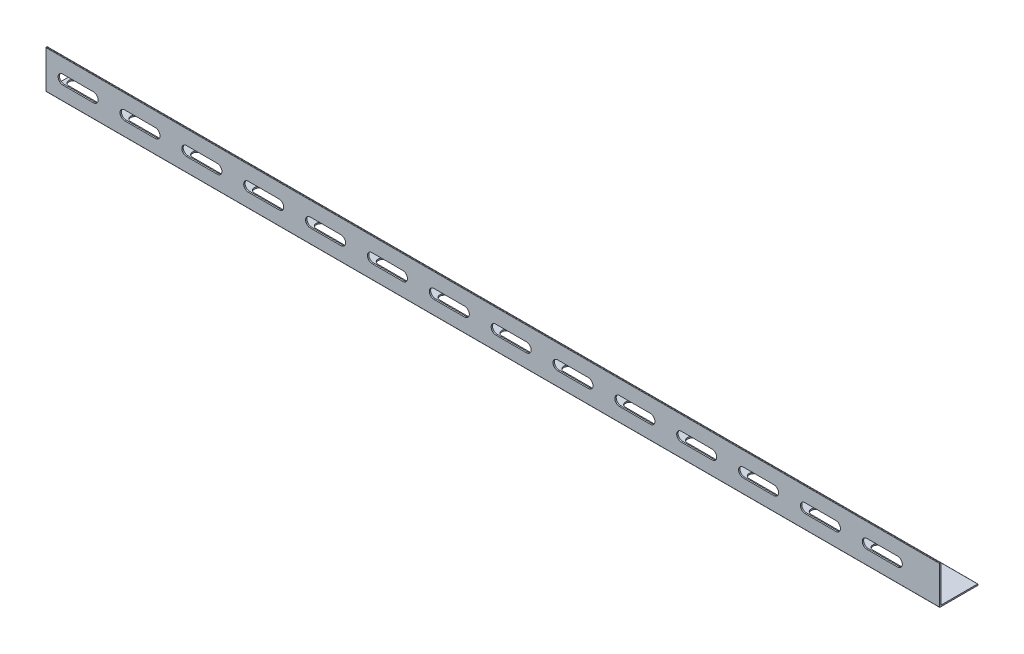
SolidWorks part; units mm, degrees
ref_plane "前视基准面" through (0, 0, 0) normal (0, 0, 1) x (1, 0, 0)
ref_plane "上视基准面" through (0, 0, 0) normal (0, 1, 0) x (1, 0, 0)
ref_plane "右视基准面" through (0, 0, 0) normal (1, 0, 0) x (0, 0, -1)
other "Configuration Table"
sketch "草图1" plane through (0, 0, 0) normal (1, 0, 0) x (0, 0, -1)
  line L1 (0, 0) -> (-5.4814, 0)
  line L2 (-4.7814, 1.3) -> (-4.7814, 27.7)
  line L3 (-5.0814, 28) -> (-5.4814, 28)
  line L4 (-5.7814, 0.3) -> (-5.7814, 27.7)
  line L5 (0, 0) -> (21.9186, 0)
  line L7 (-4.4814, 1) -> (21.9186, 1)
  line L8 (22.2186, 0.3) -> (22.2186, 0.7)
  arc A0 (-4.7814, 27.7) -> (-5.0814, 28) centre (-5.0814, 27.7) ccw
  arc A1 (-5.4814, 28) -> (-5.7814, 27.7) centre (-5.4814, 27.7) ccw
  arc A2 (21.9186, 0) -> (22.2186, 0.3) centre (21.9186, 0.3) ccw
  arc A3 (21.9186, 1) -> (22.2186, 0.7) centre (21.9186, 0.7) cw
  arc A4 (-4.7814, 1.3) -> (-4.4814, 1) centre (-4.4814, 1.3) ccw
  arc A5 (-5.4814, 0) -> (-5.7814, 0.3) centre (-5.4814, 0.3) cw
  point P10 (-4.7814, 28)
  point P13 (-5.7814, 28)
  point P16 (22.2186, 0)
  point P19 (22.2186, 1)
  point P24 (-5.7814, 0)
  dimension "D5" = 0.3
  dimension "D1" = 28
  dimension "D2" = 28
  dimension "D3" = 1
  dimension "D4" = 1
extrude "凸台-拉伸1" add sketch "草图1" along normal blind 650
sketch "草图2" plane through (0, 0, 5.7814) normal (0, 0, 1) x (1, 0, 0)
  line L0 (12.2523, 13.7143) -> (34.5086, 13.7143) construction
  line L1 (12.2523, 17.1497) -> (34.5086, 17.1497)
  line L2 (12.2523, 10.279) -> (34.5086, 10.279)
  line L3 (57.2523, 13.7143) -> (79.5086, 13.7143) construction
  line L4 (57.2523, 17.1497) -> (79.5086, 17.1497)
  line L5 (57.2523, 10.279) -> (79.5086, 10.279)
  line L6 (102.2523, 13.7143) -> (124.5086, 13.7143) construction
  line L7 (102.2523, 17.1497) -> (124.5086, 17.1497)
  line L8 (102.2523, 10.279) -> (124.5086, 10.279)
  line L9 (147.2523, 13.7143) -> (169.5086, 13.7143) construction
  line L10 (147.2523, 17.1497) -> (169.5086, 17.1497)
  line L11 (147.2523, 10.279) -> (169.5086, 10.279)
  line L12 (192.2523, 13.7143) -> (214.5086, 13.7143) construction
  line L13 (192.2523, 17.1497) -> (214.5086, 17.1497)
  line L14 (192.2523, 10.279) -> (214.5086, 10.279)
  line L15 (237.2523, 13.7143) -> (259.5086, 13.7143) construction
  line L16 (237.2523, 17.1497) -> (259.5086, 17.1497)
  line L17 (237.2523, 10.279) -> (259.5086, 10.279)
  line L18 (282.2523, 13.7143) -> (304.5086, 13.7143) construction
  line L19 (282.2523, 17.1497) -> (304.5086, 17.1497)
  line L20 (282.2523, 10.279) -> (304.5086, 10.279)
  line L21 (327.2523, 13.7143) -> (349.5086, 13.7143) construction
  line L22 (327.2523, 17.1497) -> (349.5086, 17.1497)
  line L23 (327.2523, 10.279) -> (349.5086, 10.279)
  line L24 (372.2523, 13.7143) -> (394.5086, 13.7143) construction
  line L25 (372.2523, 17.1497) -> (394.5086, 17.1497)
  line L26 (372.2523, 10.279) -> (394.5086, 10.279)
  line L27 (417.2523, 13.7143) -> (439.5086, 13.7143) construction
  line L28 (417.2523, 17.1497) -> (439.5086, 17.1497)
  line L29 (417.2523, 10.279) -> (439.5086, 10.279)
  line L30 (462.2523, 13.7143) -> (484.5086, 13.7143) construction
  line L31 (462.2523, 17.1497) -> (484.5086, 17.1497)
  line L32 (462.2523, 10.279) -> (484.5086, 10.279)
  line L33 (507.2523, 13.7143) -> (529.5086, 13.7143) construction
  line L34 (507.2523, 17.1497) -> (529.5086, 17.1497)
  line L35 (507.2523, 10.279) -> (529.5086, 10.279)
  line L36 (552.2523, 13.7143) -> (574.5086, 13.7143) construction
  line L37 (552.2523, 17.1497) -> (574.5086, 17.1497)
  line L38 (552.2523, 10.279) -> (574.5086, 10.279)
  line L39 (597.2523, 13.7143) -> (619.5086, 13.7143) construction
  line L40 (597.2523, 17.1497) -> (619.5086, 17.1497)
  line L41 (597.2523, 10.279) -> (619.5086, 10.279)
  arc A0 (12.2523, 17.1497) -> (12.2523, 10.279) centre (12.2523, 13.7143) ccw
  arc A1 (34.5086, 10.279) -> (34.5086, 17.1497) centre (34.5086, 13.7143) ccw
  arc A2 (57.2523, 17.1497) -> (57.2523, 10.279) centre (57.2523, 13.7143) ccw
  arc A3 (79.5086, 10.279) -> (79.5086, 17.1497) centre (79.5086, 13.7143) ccw
  arc A4 (102.2523, 17.1497) -> (102.2523, 10.279) centre (102.2523, 13.7143) ccw
  arc A5 (124.5086, 10.279) -> (124.5086, 17.1497) centre (124.5086, 13.7143) ccw
  arc A6 (147.2523, 17.1497) -> (147.2523, 10.279) centre (147.2523, 13.7143) ccw
  arc A7 (169.5086, 10.279) -> (169.5086, 17.1497) centre (169.5086, 13.7143) ccw
  arc A8 (192.2523, 17.1497) -> (192.2523, 10.279) centre (192.2523, 13.7143) ccw
  arc A9 (214.5086, 10.279) -> (214.5086, 17.1497) centre (214.5086, 13.7143) ccw
  arc A10 (237.2523, 17.1497) -> (237.2523, 10.279) centre (237.2523, 13.7143) ccw
  arc A11 (259.5086, 10.279) -> (259.5086, 17.1497) centre (259.5086, 13.7143) ccw
  arc A12 (282.2523, 17.1497) -> (282.2523, 10.279) centre (282.2523, 13.7143) ccw
  arc A13 (304.5086, 10.279) -> (304.5086, 17.1497) centre (304.5086, 13.7143) ccw
  arc A14 (327.2523, 17.1497) -> (327.2523, 10.279) centre (327.2523, 13.7143) ccw
  arc A15 (349.5086, 10.279) -> (349.5086, 17.1497) centre (349.5086, 13.7143) ccw
  arc A16 (372.2523, 17.1497) -> (372.2523, 10.279) centre (372.2523, 13.7143) ccw
  arc A17 (394.5086, 10.279) -> (394.5086, 17.1497) centre (394.5086, 13.7143) ccw
  arc A18 (417.2523, 17.1497) -> (417.2523, 10.279) centre (417.2523, 13.7143) ccw
  arc A19 (439.5086, 10.279) -> (439.5086, 17.1497) centre (439.5086, 13.7143) ccw
  arc A20 (462.2523, 17.1497) -> (462.2523, 10.279) centre (462.2523, 13.7143) ccw
  arc A21 (484.5086, 10.279) -> (484.5086, 17.1497) centre (484.5086, 13.7143) ccw
  arc A22 (507.2523, 17.1497) -> (507.2523, 10.279) centre (507.2523, 13.7143) ccw
  arc A23 (529.5086, 10.279) -> (529.5086, 17.1497) centre (529.5086, 13.7143) ccw
  arc A24 (552.2523, 17.1497) -> (552.2523, 10.279) centre (552.2523, 13.7143) ccw
  arc A25 (574.5086, 10.279) -> (574.5086, 17.1497) centre (574.5086, 13.7143) ccw
  arc A26 (597.2523, 17.1497) -> (597.2523, 10.279) centre (597.2523, 13.7143) ccw
  arc A27 (619.5086, 10.279) -> (619.5086, 17.1497) centre (619.5086, 13.7143) ccw
  point P2 (23.3805, 13.7143)
  point P10 (68.3805, 13.7143)
  point P18 (113.3805, 13.7143)
  point P25 (158.3805, 13.7143)
  point P32 (203.3805, 13.7143)
  point P39 (248.3805, 13.7143)
  point P46 (293.3805, 13.7143)
  point P53 (338.3805, 13.7143)
  point P60 (383.3805, 13.7143)
  point P67 (428.3805, 13.7143)
  point P74 (473.3805, 13.7143)
  point P81 (518.3805, 13.7143)
  point P88 (563.3805, 13.7143)
  point P95 (608.3805, 13.7143)
  dimension "D1" = 14
extrude "切除-拉伸1" cut sketch "草图2" against normal up to next
sketch "草图3" plane through (0, 1, 0) normal (0, 1, 0) x (1, 0, 0)
  line L0 (5.6565, 8.6331) -> (27.9128, 8.6331) construction
  line L1 (5.6565, 12.0685) -> (27.9128, 12.0685)
  line L2 (5.6565, 5.1978) -> (27.9128, 5.1978)
  line L3 (50.6565, 8.6331) -> (72.9128, 8.6331) construction
  line L4 (50.6565, 12.0685) -> (72.9128, 12.0685)
  line L5 (50.6565, 5.1978) -> (72.9128, 5.1978)
  line L6 (95.6565, 8.6331) -> (117.9128, 8.6331) construction
  line L7 (95.6565, 12.0685) -> (117.9128, 12.0685)
  line L8 (95.6565, 5.1978) -> (117.9128, 5.1978)
  line L9 (140.6565, 8.6331) -> (162.9128, 8.6331) construction
  line L10 (140.6565, 12.0685) -> (162.9128, 12.0685)
  line L11 (140.6565, 5.1978) -> (162.9128, 5.1978)
  line L12 (185.6565, 8.6331) -> (207.9128, 8.6331) construction
  line L13 (185.6565, 12.0685) -> (207.9128, 12.0685)
  line L14 (185.6565, 5.1978) -> (207.9128, 5.1978)
  line L15 (230.6565, 8.6331) -> (252.9128, 8.6331) construction
  line L16 (230.6565, 12.0685) -> (252.9128, 12.0685)
  line L17 (230.6565, 5.1978) -> (252.9128, 5.1978)
  line L18 (275.6565, 8.6331) -> (297.9128, 8.6331) construction
  line L19 (275.6565, 12.0685) -> (297.9128, 12.0685)
  line L20 (275.6565, 5.1978) -> (297.9128, 5.1978)
  line L21 (320.6565, 8.6331) -> (342.9128, 8.6331) construction
  line L22 (320.6565, 12.0685) -> (342.9128, 12.0685)
  line L23 (320.6565, 5.1978) -> (342.9128, 5.1978)
  line L24 (365.6565, 8.6331) -> (387.9128, 8.6331) construction
  line L25 (365.6565, 12.0685) -> (387.9128, 12.0685)
  line L26 (365.6565, 5.1978) -> (387.9128, 5.1978)
  line L27 (410.6565, 8.6331) -> (432.9128, 8.6331) construction
  line L28 (410.6565, 12.0685) -> (432.9128, 12.0685)
  line L29 (410.6565, 5.1978) -> (432.9128, 5.1978)
  line L30 (455.6565, 8.6331) -> (477.9128, 8.6331) construction
  line L31 (455.6565, 12.0685) -> (477.9128, 12.0685)
  line L32 (455.6565, 5.1978) -> (477.9128, 5.1978)
  line L33 (500.6565, 8.6331) -> (522.9128, 8.6331) construction
  line L34 (500.6565, 12.0685) -> (522.9128, 12.0685)
  line L35 (500.6565, 5.1978) -> (522.9128, 5.1978)
  line L36 (545.6565, 8.6331) -> (567.9128, 8.6331) construction
  line L37 (545.6565, 12.0685) -> (567.9128, 12.0685)
  line L38 (545.6565, 5.1978) -> (567.9128, 5.1978)
  line L39 (590.6565, 8.6331) -> (612.9128, 8.6331) construction
  line L40 (590.6565, 12.0685) -> (612.9128, 12.0685)
  line L41 (590.6565, 5.1978) -> (612.9128, 5.1978)
  arc A0 (5.6565, 12.0685) -> (5.6565, 5.1978) centre (5.6565, 8.6331) ccw
  arc A1 (27.9128, 5.1978) -> (27.9128, 12.0685) centre (27.9128, 8.6331) ccw
  arc A2 (50.6565, 12.0685) -> (50.6565, 5.1978) centre (50.6565, 8.6331) ccw
  arc A3 (72.9128, 5.1978) -> (72.9128, 12.0685) centre (72.9128, 8.6331) ccw
  arc A4 (95.6565, 12.0685) -> (95.6565, 5.1978) centre (95.6565, 8.6331) ccw
  arc A5 (117.9128, 5.1978) -> (117.9128, 12.0685) centre (117.9128, 8.6331) ccw
  arc A6 (140.6565, 12.0685) -> (140.6565, 5.1978) centre (140.6565, 8.6331) ccw
  arc A7 (162.9128, 5.1978) -> (162.9128, 12.0685) centre (162.9128, 8.6331) ccw
  arc A8 (185.6565, 12.0685) -> (185.6565, 5.1978) centre (185.6565, 8.6331) ccw
  arc A9 (207.9128, 5.1978) -> (207.9128, 12.0685) centre (207.9128, 8.6331) ccw
  arc A10 (230.6565, 12.0685) -> (230.6565, 5.1978) centre (230.6565, 8.6331) ccw
  arc A11 (252.9128, 5.1978) -> (252.9128, 12.0685) centre (252.9128, 8.6331) ccw
  arc A12 (275.6565, 12.0685) -> (275.6565, 5.1978) centre (275.6565, 8.6331) ccw
  arc A13 (297.9128, 5.1978) -> (297.9128, 12.0685) centre (297.9128, 8.6331) ccw
  arc A14 (320.6565, 12.0685) -> (320.6565, 5.1978) centre (320.6565, 8.6331) ccw
  arc A15 (342.9128, 5.1978) -> (342.9128, 12.0685) centre (342.9128, 8.6331) ccw
  arc A16 (365.6565, 12.0685) -> (365.6565, 5.1978) centre (365.6565, 8.6331) ccw
  arc A17 (387.9128, 5.1978) -> (387.9128, 12.0685) centre (387.9128, 8.6331) ccw
  arc A18 (410.6565, 12.0685) -> (410.6565, 5.1978) centre (410.6565, 8.6331) ccw
  arc A19 (432.9128, 5.1978) -> (432.9128, 12.0685) centre (432.9128, 8.6331) ccw
  arc A20 (455.6565, 12.0685) -> (455.6565, 5.1978) centre (455.6565, 8.6331) ccw
  arc A21 (477.9128, 5.1978) -> (477.9128, 12.0685) centre (477.9128, 8.6331) ccw
  arc A22 (500.6565, 12.0685) -> (500.6565, 5.1978) centre (500.6565, 8.6331) ccw
  arc A23 (522.9128, 5.1978) -> (522.9128, 12.0685) centre (522.9128, 8.6331) ccw
  arc A24 (545.6565, 12.0685) -> (545.6565, 5.1978) centre (545.6565, 8.6331) ccw
  arc A25 (567.9128, 5.1978) -> (567.9128, 12.0685) centre (567.9128, 8.6331) ccw
  arc A26 (590.6565, 12.0685) -> (590.6565, 5.1978) centre (590.6565, 8.6331) ccw
  arc A27 (612.9128, 5.1978) -> (612.9128, 12.0685) centre (612.9128, 8.6331) ccw
  point P2 (16.7847, 8.6331)
  point P10 (61.7847, 8.6331)
  point P18 (106.7847, 8.6331)
  point P25 (151.7847, 8.6331)
  point P32 (196.7847, 8.6331)
  point P39 (241.7847, 8.6331)
  point P46 (286.7847, 8.6331)
  point P53 (331.7847, 8.6331)
  point P60 (376.7847, 8.6331)
  point P67 (421.7847, 8.6331)
  point P74 (466.7847, 8.6331)
  point P81 (511.7847, 8.6331)
  point P88 (556.7847, 8.6331)
  point P95 (601.7847, 8.6331)
  dimension "D1" = 14
extrude "切除-拉伸2" cut sketch "草图3" against normal up to next
